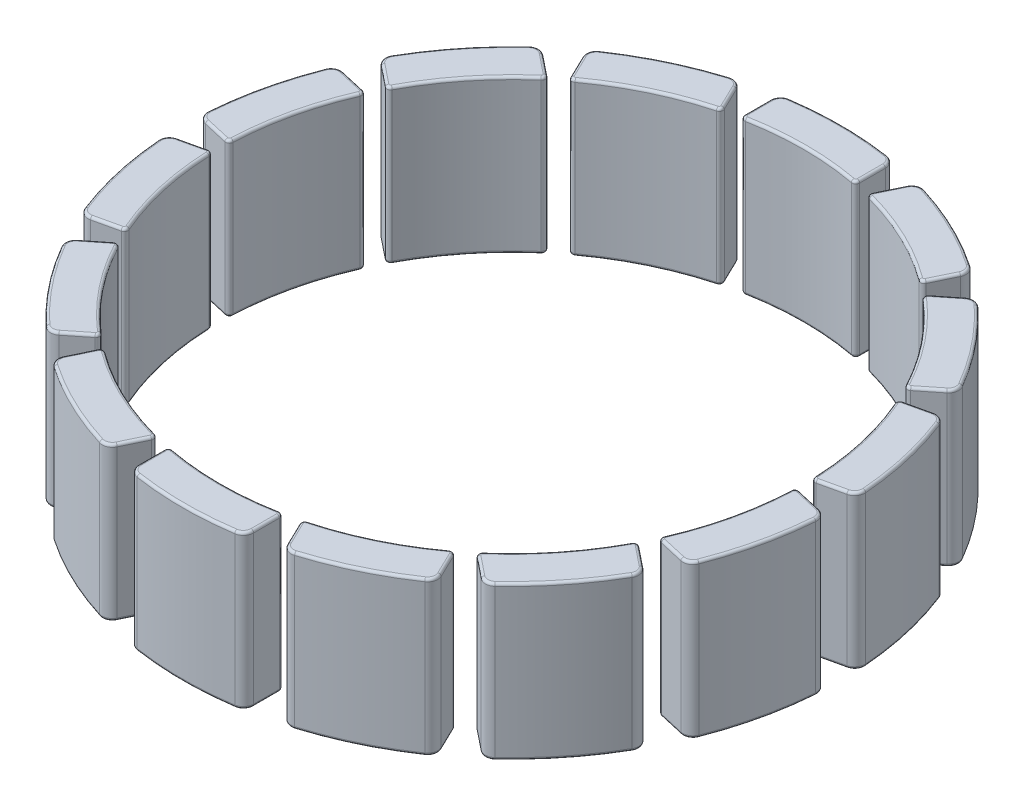
SolidWorks part; units mm, degrees
ref_plane "Alzado" through (0, 0, 0) normal (0, 0, 1) x (1, 0, 0)
ref_plane "Planta" through (0, 0, 0) normal (0, 1, 0) x (1, 0, 0)
ref_plane "Vista lateral" through (0, 0, 0) normal (1, 0, 0) x (0, 0, -1)
sketch "Croquis1" plane through (0, 0, 0) normal (0, 1, 0) x (1, 0, 0)
  line L0 (0, 16.0672) -> (0, -15.7232) construction
  line L1 (-15.3447, 0) -> (15.4135, 0) construction
  line L2 (-2.25, -11.3575) -> (-2.25, -12.3623)
  line L3 (2.25, -12.3623) -> (2.25, -11.3575)
  arc A0 (-1.9092, -12.7579) -> (1.9092, -12.7579) centre (0, 0) ccw
  arc A1 (-2.0727, -11.21) -> (2.0727, -11.21) centre (0, 0) ccw
  arc A2 (-2.25, -12.3623) -> (-1.9092, -12.7579) centre (-1.85, -12.3623) ccw
  arc A3 (2.25, -12.3623) -> (1.9092, -12.7579) centre (1.85, -12.3623) cw
  arc A4 (2.25, -11.3575) -> (2.0727, -11.21) centre (2.1, -11.3575) ccw
  arc A5 (-2.25, -11.3575) -> (-2.0727, -11.21) centre (-2.1, -11.3575) cw
  dimension "D3" = 0.4
  dimension "D4" = 0.15
  dimension "D5" = 12.9
  dimension "D6" = 11.4
  dimension "D1" = 4.5
  dimension "D2" = 4.5
extrude "Saliente-Extruir1" add sketch "Croquis1" along normal blind 6
fillet "Redondeo1" radius 0.1 16 edges at (0, 0, 12.9) (2.1531, 0, 12.6234) (2.25, 0, 11.8599) (2.1959, 0, 11.2422) (0, 0, 11.4) (-2.1959, 0, 11.2422) (-2.25, 0, 11.8599) (-2.1531, 0, 12.6234) (-2.25, 6, 11.8599) (-2.1959, 6, 11.2422) (0, 6, 11.4) (2.1959, 6, 11.2422) (2.25, 6, 11.8599) (2.1531, 6, 12.6234) (0, 6, 12.9) (-2.1531, 6, 12.6234)
pattern_circular "MatrizC3" count 14 over 360 about axis through (0, 0, 0) along (0, 1, 0) of bodies 101
